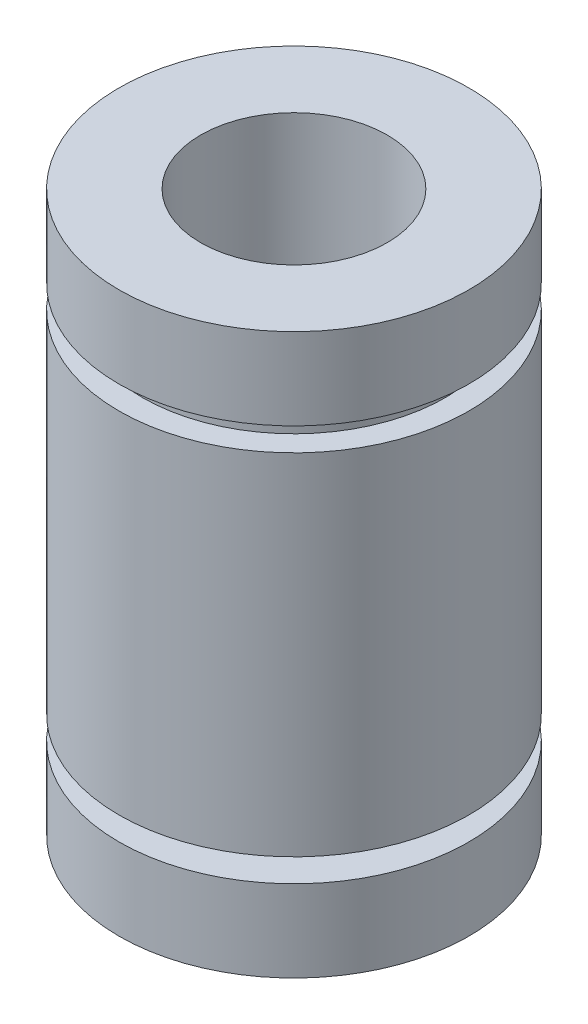
SolidWorks part; units mm, degrees
ref_plane "Alzado" through (0, 0, 0) normal (0, 0, 1) x (1, 0, 0)
ref_plane "Planta" through (0, 0, 0) normal (0, 1, 0) x (1, 0, 0)
ref_plane "Vista lateral" through (0, 0, 0) normal (1, 0, 0) x (0, 0, -1)
sketch "Croquis3" plane through (0, 0, 0) normal (1, 0, 0) x (0, 0, -1)
  line L0 (0, 0) -> (0, 15.0962) construction
  line L1 (0, 0) -> (0, -12.5) construction
  line L2 (-7.5, 0) -> (-4, 0)
  line L3 (-7.5, 0) -> (-7.5, -3.5)
  line L4 (-7.5, -3.5) -> (-6.5, -3.5)
  line L5 (-6.5, -3.5) -> (-6.5, -4.5)
  line L6 (-6.5, -4.5) -> (-7.5, -4.5)
  line L7 (-7.5, -4.5) -> (-7.5, -19.5)
  line L8 (-7.5, -19.5) -> (-5.75, -19.5)
  line L9 (-5.75, -19.5) -> (-5.75, -20.5)
  line L10 (-5.75, -20.5) -> (-7.5, -20.5)
  line L11 (-7.5, -20.5) -> (-7.5, -24)
  line L12 (-7.5, -24) -> (-4, -24)
  line L13 (-4, 0) -> (-4, -24)
  dimension "D1" = 7.5
  dimension "D2" = 4
  dimension "D3" = 3.5
  dimension "D4" = 1
  dimension "D5" = 1
  dimension "D6" = 15
  dimension "D7" = 1
  dimension "D8" = 3.5
  dimension "D9" = 4
revolve "Revolución2" add sketch "Croquis3" angle 360 about L1
